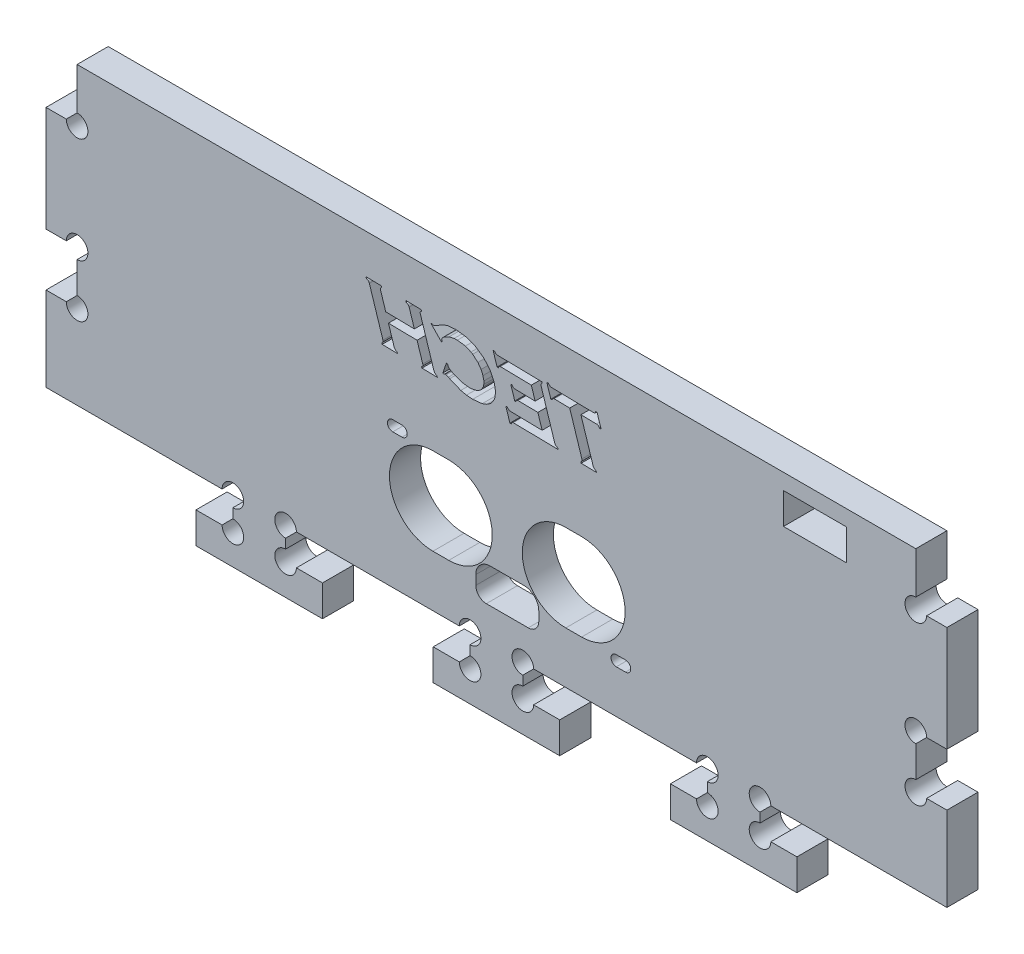
SolidWorks part; units mm, degrees
ref_plane "Front Plane" through (0, 0, 0) normal (0, 0, 1) x (1, 0, 0)
ref_plane "Top Plane" through (0, 0, 0) normal (0, 1, 0) x (1, 0, 0)
ref_plane "Right Plane" through (0, 0, 0) normal (1, 0, 0) x (0, 0, -1)
sketch "Sketch1" plane through (0, 0, 0) normal (0, 0, 1) x (1, 0, 0)
  line L1 (85.45, -35) -> (-85.45, -35)
  line L2 (85.45, -35) -> (85.45, 35)
  line L3 (85.45, 35) -> (-85.45, 35)
  line L4 (-85.45, -35) -> (-85.45, 35)
  line L5 (85.45, -35) -> (-85.45, 35) construction
  line L6 (85.45, 35) -> (-85.45, -35) construction
  point P0 (0, 0)
  dimension "D1" = 170.9
  dimension "D2" = 70
extrude "Boss-Extrude1" add sketch "Sketch1" along normal blind 5.9
sketch "Sketch2" plane through (0, 0, 5.9) normal (0, 0, 1) x (1, 0, 0)
  line L0 (-85.45, 35) -> (-85.45, -35) construction
  line L1 (-85.45, -21) -> (85.45, -21)
  line L2 (-85.45, -21) -> (-85.45, -35)
  line L3 (-85.45, -35) -> (85.45, -35)
  line L4 (85.45, -21) -> (85.45, -35)
  line L5 (-50, -21) -> (-50, -26.9)
  line L6 (-50, -26.9) -> (-57, -26.9)
  line L7 (-57, -26.9) -> (-57, -32.8)
  line L8 (-57, -32.8) -> (-33, -32.8)
  line L9 (-33, -32.8) -> (-33, -26.9)
  line L10 (-33, -26.9) -> (-40, -26.9)
  line L11 (-40, -26.9) -> (-40, -21)
  line L12 (-40, -21) -> (-50, -21)
  line L13 (-50, -26.9) -> (-40, -26.9) construction
  line L14 (-5, -26.9) -> (5, -26.9) construction
  line L16 (-5, -21) -> (-5, -26.9)
  line L17 (-12, -26.9) -> (-12, -32.8)
  line L18 (-12, -32.8) -> (12, -32.8)
  line L19 (12, -32.8) -> (12, -26.9)
  line L20 (12, -26.9) -> (5, -26.9)
  line L21 (5, -26.9) -> (5, -21)
  line L22 (-5, -26.9) -> (-12, -26.9)
  line L23 (40, -21) -> (40, -26.9)
  line L24 (33, -26.9) -> (33, -32.8)
  line L25 (33, -32.8) -> (57, -32.8)
  line L26 (57, -32.8) -> (57, -26.9)
  line L27 (57, -26.9) -> (50, -26.9)
  line L28 (50, -26.9) -> (50, -21)
  line L29 (40, -26.9) -> (33, -26.9)
  point P9 (-45, -26.9)
  point P16 (-45, -32.8)
  point P17 (0, -26.9)
  point P22 (-5, -23.95)
  line M23 (-85.45, 35) -> (-85.45, -35)
  line M24 (-85.45, -35) -> (85.45, -35)
  line M25 (85.45, -35) -> (85.45, 35)
  dimension "D1" = 14
  dimension "D2" = 10
  dimension "D3" = 5.9
  dimension "D4" = 5.9
  dimension "D5" = 24
  dimension "D7" = 35
  dimension "D6" = 3
extrude "Cut-Extrude1" cut sketch "Sketch2" against normal through all contours L29 L23 L1 L21 L20 L19 L18 L17 L22 L16 L11 L10 L9 L8 L7 L6 L5 L28 L27 L26 L25 L24 M23 M24 M25
sketch "Sketch3" plane through (0, 0, 5.9) normal (0, 0, 1) x (1, 0, 0)
  line L0 (85.45, -21) -> (85.45, 35) construction
  line L1 (85.45, 35) -> (79.55, 35)
  line L2 (85.45, 35) -> (85.45, 25)
  line L3 (85.45, 25) -> (79.55, 25)
  line L4 (79.55, 35) -> (79.55, 25)
  line L5 (79.55, 25) -> (79.55, -5) construction
  line L10 (85.45, 35) -> (-85.45, 35) construction
  line L11 (0, 0) -> (0, 32.6921) construction
  line L12 (-79.55, 25) -> (-79.55, -5) construction
  line L16 (-85.45, -5) -> (-79.55, -5)
  line L17 (-79.55, 35) -> (-79.55, 25)
  line L18 (-85.45, 25) -> (-79.55, 25)
  line L19 (-85.45, 35) -> (-85.45, 25)
  line L20 (-85.45, 35) -> (-79.55, 35)
  line L21 (85.45, -5) -> (85.45, 5)
  line L22 (-85.45, -5) -> (-79.55, -5) construction
  line L23 (-85.45, -5) -> (-85.45, 5)
  line L24 (-85.45, 5) -> (-79.55, 5)
  line L25 (-79.55, -5) -> (-79.55, 5)
  line L26 (-85.45, -5) -> (-79.55, 5) construction
  line L27 (-85.45, 5) -> (-79.55, -5) construction
  line L28 (85.45, 5) -> (79.55, 5)
  line L29 (79.55, -5) -> (79.55, 5)
  line L30 (85.45, -5) -> (79.55, -5)
  point P26 (-82.5, 0)
  dimension "D4" = 5.9
  dimension "D1" = 10
  dimension "D2" = 5.9
  dimension "D5" = 10
  dimension "D3" = 20
extrude "Cut-Extrude2" cut sketch "Sketch3" against normal through all
sketch "Sketch4" plane through (0, 0, 0) normal (0, 0, 1) x (1, 0, 0)
  line L151 (-9.2284, 20.7899) -> (-9.2478, 20.8809)
  line L152 (-9.2034, 20.6979) -> (-9.2284, 20.7899)
  line L153 (-9.115, 20.5235) -> (-9.2034, 20.6979)
  line L154 (-8.9684, 20.3663) -> (-9.115, 20.5235)
  line L155 (-8.7515, 20.205) -> (-8.9684, 20.3663)
  line L156 (-8.1394, 19.87) -> (-8.7515, 20.205)
  line L157 (-6.7329, 19.3329) -> (-8.1394, 19.87)
  line L158 (-5.2731, 19.1203) -> (-6.7329, 19.3329)
  line L159 (-4.6186, 19.1457) -> (-5.2731, 19.1203)
  line L160 (-3.8293, 19.3102) -> (-4.6186, 19.1457)
  line L161 (-3.3106, 19.5543) -> (-3.8293, 19.3102)
  line L162 (-2.9081, 19.8946) -> (-3.3106, 19.5543)
  line L163 (-2.711, 20.1493) -> (-2.9081, 19.8946)
  line L164 (-2.5061, 20.5517) -> (-2.711, 20.1493)
  line L165 (-2.3939, 21.0234) -> (-2.5061, 20.5517)
  line L166 (-2.3873, 21.5946) -> (-2.3939, 21.0234)
  line L167 (-2.5583, 22.3849) -> (-2.3873, 21.5946)
  line L168 (-2.9166, 23.2153) -> (-2.5583, 22.3849)
  line L169 (-3.5306, 24.0707) -> (-2.9166, 23.2153)
  line L170 (-4.5179, 24.9155) -> (-3.5306, 24.0707)
  line L171 (-4.8408, 25.1146) -> (-4.5179, 24.9155)
  line L172 (-5.9046, 25.5642) -> (-4.8408, 25.1146)
  line L173 (-7.409, 25.7815) -> (-5.9046, 25.5642)
  line L174 (-8.016, 25.7573) -> (-7.409, 25.7815)
  line L175 (-8.9781, 25.5417) -> (-8.016, 25.7573)
  line L176 (-9.8198, 25.1115) -> (-8.9781, 25.5417)
  line L177 (-10.1086, 24.8941) -> (-9.8198, 25.1115)
  line L178 (-10.2694, 24.7306) -> (-10.1086, 24.8941)
  line L179 (-10.3378, 24.6245) -> (-10.2694, 24.7306)
  line L180 (-10.3698, 24.536) -> (-10.3378, 24.6245)
  line L181 (-10.3798, 24.4389) -> (-10.3698, 24.536)
  line L182 (-10.3557, 24.295) -> (-10.3798, 24.4389)
  line L183 (-10.2804, 24.1011) -> (-10.3557, 24.295)
  line L184 (-12.1888, 26.0706) -> (-12.2674, 26.1251)
  line L185 (-12.0044, 25.9661) -> (-12.1888, 26.0706)
  line L186 (-11.8857, 25.9362) -> (-12.0044, 25.9661)
  line L187 (-11.7809, 25.9622) -> (-11.8857, 25.9362)
  line L188 (-11.5724, 26.0725) -> (-11.7809, 25.9622)
  line L189 (-11.284, 26.2569) -> (-11.5724, 26.0725)
  line L190 (-10.0293, 26.9841) -> (-11.284, 26.2569)
  line L191 (-9.1433, 27.269) -> (-10.0293, 26.9841)
  line L192 (-7.671, 27.3758) -> (-9.1433, 27.269)
  line L193 (-5.6736, 27.1202) -> (-7.671, 27.3758)
  line L194 (-4.0176, 26.4929) -> (-5.6736, 27.1202)
  line L195 (-2.4233, 25.3757) -> (-4.0176, 26.4929)
  line L196 (-1.2352, 24.0059) -> (-2.4233, 25.3757)
  line L197 (-0.4413, 22.3521) -> (-1.2352, 24.0059)
  line L198 (-0.3755, 22.1308) -> (-0.4413, 22.3521)
  line L199 (-0.1833, 20.9848) -> (-0.3755, 22.1308)
  line L200 (-0.2643, 20.0389) -> (-0.1833, 20.9848)
  line L201 (-0.3851, 19.6209) -> (-0.2643, 20.0389)
  line L202 (-0.6675, 19.054) -> (-0.3851, 19.6209)
  line L203 (-1.1209, 18.52) -> (-0.6675, 19.054)
  line L204 (-1.8307, 18.0241) -> (-1.1209, 18.52)
  line L205 (-2.707, 17.6972) -> (-1.8307, 18.0241)
  line L206 (-4.5042, 17.5171) -> (-2.707, 17.6972)
  line L207 (-5.691, 17.6085) -> (-4.5042, 17.5171)
  line L208 (-6.7588, 17.8456) -> (-5.691, 17.6085)
  line L209 (-8.8674, 18.7173) -> (-6.7588, 17.8456)
  line L210 (-9.1249, 18.8406) -> (-8.8674, 18.7173)
  line L211 (-9.5294, 19.0135) -> (-9.1249, 18.8406)
  line L212 (-9.6813, 19.0544) -> (-9.5294, 19.0135)
  line L213 (-12.4104, 26.0013) -> (-12.2674, 26.1251)
  line L214 (-10.4296, 23.9754) -> (-12.4104, 26.0013)
  line L215 (-10.2804, 24.1011) -> (-10.4296, 23.9754)
  line L216 (-9.4814, 21.0174) -> (-9.2478, 20.8809)
  line L217 (-10.1685, 19.007) -> (-9.4814, 21.0174)
  line L218 (-9.9471, 18.8831) -> (-10.1685, 19.007)
  line L219 (-15.0584, 21.9407) -> (-13.9787, 18.5705)
  line L220 (-20.4883, 22.0355) -> (-15.0584, 21.9407)
  line L221 (-19.4087, 18.6653) -> (-20.4883, 22.0355)
  line L222 (-18.7679, 17.8986) -> (-18.8544, 18.1651)
  line L223 (-21.6816, 17.9494) -> (-18.7679, 17.8986)
  line L224 (-21.768, 18.2159) -> (-21.6816, 17.9494)
  line L225 (-24.1131, 26.7665) -> (-21.5296, 18.7106)
  line L226 (-24.7557, 27.5416) -> (-24.6714, 27.2751)
  line L227 (-21.8421, 27.4907) -> (-24.7557, 27.5416)
  line L228 (-21.7577, 27.2243) -> (-21.8421, 27.4907)
  line L229 (-21.0007, 23.6341) -> (-21.9921, 26.7254)
  line L230 (-15.5707, 23.5394) -> (-21.0007, 23.6341)
  line L231 (-16.5621, 26.6306) -> (-15.5707, 23.5394)
  line L232 (-17.2068, 27.4098) -> (-17.1224, 27.1434)
  line L233 (-14.2931, 27.3589) -> (-17.2068, 27.4098)
  line L234 (-14.2088, 27.0925) -> (-14.2931, 27.3589)
  line L235 (-11.8605, 18.5383) -> (-14.4451, 26.5978)
  line L236 (-11.219, 17.7668) -> (-11.3054, 18.0333)
  line L237 (-14.1326, 17.8177) -> (-11.219, 17.7668)
  line L238 (-14.219, 18.0841) -> (-14.1326, 17.8177)
  line L239 (11.0482, 18.1482) -> (8.4687, 26.1916)
  line L240 (11.6928, 17.3669) -> (11.6064, 17.6334)
  line L241 (3.1816, 17.5155) -> (11.6928, 17.3669)
  line L242 (2.5497, 17.1291) -> (2.8146, 17.1244)
  line L243 (1.7822, 19.5271) -> (2.5497, 17.1291)
  line L244 (2.0471, 19.5224) -> (1.7822, 19.5271)
  line L245 (8.6642, 19.0095) -> (2.6672, 19.1142)
  line L246 (7.8534, 21.5407) -> (8.6642, 19.0095)
  line L247 (4.1038, 21.6062) -> (7.8534, 21.5407)
  line L248 (3.4781, 21.2197) -> (3.743, 21.2151)
  line L249 (2.7085, 23.6177) -> (3.4781, 21.2197)
  line L250 (2.9734, 23.6131) -> (2.7085, 23.6177)
  line L251 (7.3411, 23.1394) -> (3.5914, 23.2049)
  line L252 (6.6147, 25.4042) -> (7.3411, 23.1394)
  line L253 (0.7523, 25.5066) -> (6.6147, 25.4042)
  line L254 (0.1204, 25.1202) -> (0.3853, 25.1155)
  line L255 (-0.6471, 27.5182) -> (0.1204, 25.1202)
  line L256 (-0.3822, 27.5136) -> (-0.6471, 27.5182)
  line L257 (8.6187, 26.959) -> (0.242, 27.1052)
  line L258 (8.703, 26.6926) -> (8.6187, 26.959)
  line L259 (10.4521, 26.927) -> (18.446, 26.7875)
  line L260 (9.5506, 27.3402) -> (9.8155, 27.3356)
  line L261 (10.3181, 24.9422) -> (9.5506, 27.3402)
  line L262 (10.583, 24.9375) -> (10.3181, 24.9422)
  line L263 (13.8988, 25.2771) -> (10.9624, 25.3284)
  line L264 (16.2113, 18.0601) -> (13.8988, 25.2771)
  line L265 (16.0633, 17.2906) -> (15.9769, 17.5571)
  line L266 (18.9769, 17.2398) -> (16.0633, 17.2906)
  line L267 (18.8905, 17.5062) -> (18.9769, 17.2398)
  line L268 (16.0178, 25.2401) -> (18.3303, 18.0231)
  line L269 (18.9604, 25.1888) -> (16.0178, 25.2401)
  line L270 (19.8537, 24.7757) -> (19.5888, 24.7803)
  line L271 (19.0862, 27.1737) -> (19.8537, 24.7757)
  line L272 (18.8213, 27.1784) -> (19.0862, 27.1737)
  arc A38 (-9.9471, 18.8831) -> (-9.6813, 19.0544) centre (-9.5869, 18.616) cw
  arc A39 (-13.9787, 18.5705) -> (-14.219, 18.0841) centre (-14.2792, 18.4165) cw
  arc A40 (-18.8544, 18.1651) -> (-19.4087, 18.6653) centre (-18.6877, 18.907) cw
  arc A41 (-21.5296, 18.7106) -> (-21.768, 18.2159) centre (-21.8962, 18.5825) cw
  arc A42 (-24.6714, 27.2751) -> (-24.1131, 26.7665) centre (-24.8131, 26.5588) cw
  arc A43 (-21.9921, 26.7254) -> (-21.7577, 27.2243) centre (-21.6254, 26.8576) cw
  arc A44 (-17.1224, 27.1434) -> (-16.5621, 26.6306) centre (-17.2563, 26.4345) cw
  arc A45 (-14.4451, 26.5978) -> (-14.2088, 27.0925) centre (-14.1402, 26.7559) cw
  arc A46 (-11.3054, 18.0333) -> (-11.8605, 18.5383) centre (-11.1443, 18.768) cw
  arc A47 (8.4687, 26.1916) -> (8.703, 26.6926) centre (8.7777, 26.3523) cw
  arc A48 (11.6064, 17.6334) -> (11.0482, 18.1482) centre (11.7666, 18.3671) cw
  arc A49 (2.8146, 17.1244) -> (3.1816, 17.5155) centre (3.1936, 17.1364) cw
  arc A50 (2.6672, 19.1142) -> (2.0471, 19.5224) centre (2.7334, 19.8898) cw
  arc A51 (3.743, 21.2151) -> (4.1038, 21.6062) centre (4.119, 21.2302) cw
  arc A52 (3.5914, 23.2049) -> (2.9734, 23.6131) centre (3.5676, 23.8407) cw
  arc A53 (0.3853, 25.1155) -> (0.7523, 25.5066) centre (0.7643, 25.1276) cw
  arc A54 (0.242, 27.1052) -> (-0.3822, 27.5136) centre (0.3246, 27.9128) cw
  arc A55 (18.446, 26.7875) -> (18.8213, 27.1784) centre (18.5112, 27.1005) ccw
  arc A56 (9.8155, 27.3356) -> (10.4521, 26.927) centre (10.653, 27.9403) ccw
  arc A57 (10.9624, 25.3284) -> (10.583, 24.9375) centre (10.9681, 24.9432) ccw
  arc A58 (15.9769, 17.5571) -> (16.2113, 18.0601) centre (15.9285, 17.8858) ccw
  arc A59 (18.3303, 18.0231) -> (18.8905, 17.5062) centre (19.0545, 18.2459) ccw
  arc A60 (19.5888, 24.7803) -> (18.9604, 25.1888) centre (18.9367, 24.4646) ccw
  point P606 (18.8213, 27.1784)
  point P607 (18.446, 26.7875)
  point P608 (10.4521, 26.927)
  point P609 (9.8155, 27.3356)
  point P610 (9.5506, 27.3402)
  point P611 (10.3181, 24.9422)
  point P612 (10.583, 24.9375)
  point P613 (10.9624, 25.3284)
  point P614 (13.8988, 25.2771)
  point P615 (16.2113, 18.0601)
  point P616 (15.9769, 17.5571)
  point P617 (16.0633, 17.2906)
  point P618 (18.9769, 17.2398)
  point P619 (18.8905, 17.5062)
  point P620 (18.3303, 18.0231)
  point P621 (16.0178, 25.2401)
  point P622 (18.9604, 25.1888)
  point P623 (19.5888, 24.7803)
  point P624 (19.8537, 24.7757)
  point P625 (19.0862, 27.1737)
extrude "Cut-Extrude5" cut sketch "Sketch4" along normal up to next
sketch "Sketch5" plane through (0, 0, 5.9) normal (0, 0, 1) x (1, 0, 0)
  circle A0 centre (-50, -26.9) radius 2.05
  circle A1 centre (-40, -26.9) radius 2.05
  circle A2 centre (-5, -26.9) radius 2.05
  circle A3 centre (5, -26.9) radius 2.05
  circle A4 centre (40, -26.9) radius 2.05
  circle A5 centre (50, -26.9) radius 2.05
  circle A6 centre (50, -21) radius 2.05
  circle A7 centre (40, -21) radius 2.05
  circle A8 centre (5, -21) radius 2.05
  circle A9 centre (-5, -21) radius 2.05
  circle A10 centre (-40, -21) radius 2.05
  circle A11 centre (-50, -21) radius 2.05
  circle A12 centre (-79.55, -5) radius 2.05
  circle A13 centre (-79.55, 5) radius 2.05
  circle A14 centre (-79.55, 25) radius 2.05
  circle A15 centre (79.55, 25) radius 2.05
  circle A16 centre (79.55, 5) radius 2.05
  circle A17 centre (79.55, -5) radius 2.05
  dimension "D1" = 4.1
extrude "Cut-Extrude6" cut sketch "Sketch5" against normal up to next
sketch "Sketch6" plane through (0, 0, 0) normal (0, 0, -1) x (-1, 0, 0)
  line L0 (-79.55, 35) -> (79.55, 35) construction
  line L1 (-66.45, 32) -> (-54.45, 32)
  line L2 (-66.45, 32) -> (-66.45, 26.1)
  line L3 (-66.45, 26.1) -> (-54.45, 26.1)
  line L4 (-54.45, 32) -> (-54.45, 26.1)
  line L5 (-66.45, 32) -> (-54.45, 26.1) construction
  line L6 (-66.45, 26.1) -> (-54.45, 32) construction
  line L9 (-85.45, 5) -> (-85.45, 25) construction
  point P4 (-60.45, 29.05)
  dimension "D2" = 5.9
  dimension "D1" = 12
  dimension "D3" = 3
  dimension "D4" = 25
extrude "Cut-Extrude7" cut sketch "Sketch6" against normal up to next
sketch "Sketch8" plane through (0, 0, 0) normal (0, 0, -1) x (-1, 0, 0)
  line L23 (-8.0282, -12.7653) -> (-8.0282, -10.9903)
  line L24 (-5.2532, -8.2153) -> (1.1468, -8.2153)
  line L25 (3.9218, -10.9903) -> (3.9218, -12.7653)
  line L29 (12.0468, 5.2847) -> (9.0468, 5.2847)
  line L30 (9.0468, -11.2153) -> (12.0468, -11.2153)
  line L31 (-13.1532, 5.2847) -> (-16.1532, 5.2847)
  line L32 (-16.1532, -11.2153) -> (-13.1532, -11.2153)
  line L33 (-24.4782, -12.8153) -> (-22.7282, -12.8153)
  line L34 (-22.7282, -10.8153) -> (-24.4782, -10.8153)
  line L35 (17.9218, 4.5847) -> (19.6718, 4.5847)
  line L36 (19.6718, 6.5847) -> (17.9218, 6.5847)
  line L37 (-79.55, 2.95) -> (-79.55, -2.95) construction
  line L38 (-54.45, 32) -> (-66.45, 32) construction
  line L41 (-6.0282, -14.7653) -> (1.9218, -14.7653)
  arc A10 (-5.2532, -8.2153) -> (-8.0282, -10.9903) centre (-5.2532, -10.9903) ccw
  arc A11 (3.9218, -10.9903) -> (1.1468, -8.2153) centre (1.1468, -10.9903) ccw
  arc A12 (9.0468, 5.2847) -> (9.0468, -11.2153) centre (9.0468, -2.9653) ccw
  arc A13 (12.0468, -11.2153) -> (12.0468, 5.2847) centre (12.0468, -2.9653) ccw
  arc A14 (-16.1532, 5.2847) -> (-16.1532, -11.2153) centre (-16.1532, -2.9653) ccw
  arc A15 (-13.1532, -11.2153) -> (-13.1532, 5.2847) centre (-13.1532, -2.9653) ccw
  arc A16 (-22.7282, -12.8153) -> (-22.7282, -10.8153) centre (-22.7282, -11.8153) ccw
  arc A17 (-24.4782, -10.8153) -> (-24.4782, -12.8153) centre (-24.4782, -11.8153) ccw
  arc A18 (19.6718, 4.5847) -> (19.6718, 6.5847) centre (19.6718, 5.5847) ccw
  arc A19 (17.9218, 6.5847) -> (17.9218, 4.5847) centre (17.9218, 5.5847) ccw
  arc A20 (1.9218, -14.7653) -> (3.9218, -12.7653) centre (1.9218, -12.7653) ccw
  arc A21 (-8.0282, -12.7653) -> (-6.0282, -14.7653) centre (-6.0282, -12.7653) ccw
  point P4 (-8.0282, -11.8778)
  point P5 (3.9218, -11.8778)
  dimension "D1" = 2
  dimension "D2" = 2.775
  dimension "D3" = 8.25
  dimension "D4" = 1
  dimension "D5" = 55.0718
  dimension "D6" = 56.8218
  dimension "D7" = 63.3968
  dimension "D8" = 66.3968
  dimension "D9" = 71.5218
  dimension "D10" = 83.4718
  dimension "D11" = 88.5968
  dimension "D12" = 97.4718
  dimension "D13" = 26.4153
  dimension "D14" = 34.9653
  dimension "D15" = 40.2153
  dimension "D16" = 43.8153
  dimension "D17" = 43.8778
extrude "Cut-Extrude9" cut sketch "Sketch8" against normal up to next
equation "\"e\" = 5.9"
equation "\"D1@Boss-Extrude1\"=\"e\""
equation "\"D3@Sketch2\"= \"e\""
equation "\"D4@Sketch2\"= \"e\""
equation "\"D2@Sketch3\"= \"e\""
equation "\"D4@Sketch3\"= \"e\""
equation "\"D2@Sketch6\"= \"e\""
equation "\"D1@Sketch1\"= 165 + \"e\""
